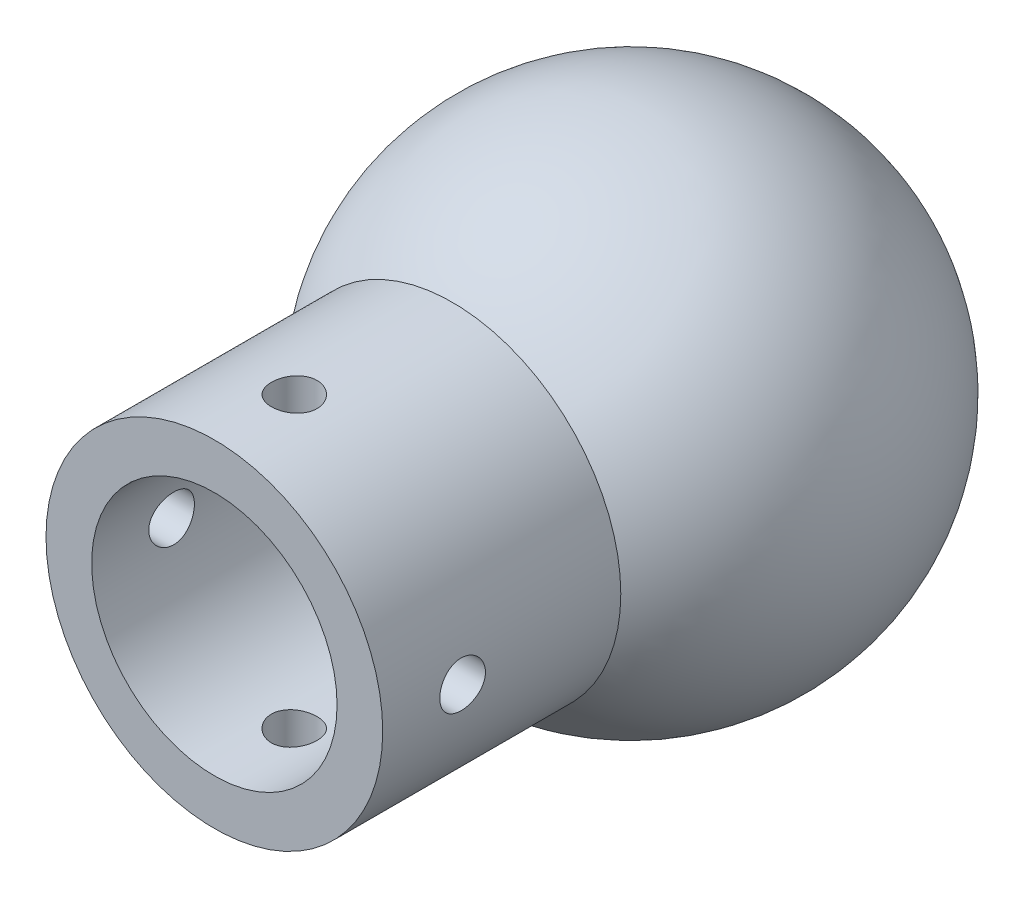
SolidWorks part; units mm, degrees
ref_plane "Front Plane" through (0, 0, 0) normal (0, 0, 1) x (1, 0, 0)
ref_plane "Top Plane" through (0, 0, 0) normal (0, 1, 0) x (1, 0, 0)
ref_plane "Right Plane" through (0, 0, 0) normal (1, 0, 0) x (0, 0, -1)
sketch "Sketch1" plane through (0, 0, 0) normal (0, 0, 1) x (1, 0, 0)
  line L0 (0, 21.5) -> (0, -21.5)
  arc A0 (0, -21.5) -> (0, 21.5) centre (0, 0) ccw
  dimension "D1" = 43
revolve "Revolve1" add sketch "Sketch1" angle 360 about L0
ref_plane "Plane1" through (0, 0, 21.5) normal (0, 0, 1) x (1, 0, 0)
sketch "Sketch2" plane through (0, 0, 21.5) normal (0, 0, 1) x (1, 0, 0)
  circle A0 centre (0, 0) radius 10.75
  dimension "D1" = 21.5
extrude "Cut-Extrude1" cut sketch "Sketch2" against normal blind 15
sketch "Sketch3" plane through (0, 0, 21.5) normal (0, 0, 1) x (1, 0, 0)
  circle A0 centre (0, 0) radius 10.75
  circle A1 centre (0, 0) radius 14.75
  dimension "D1" = 4
extrude "Boss-Extrude1" add sketch "Sketch3" against normal up to surface (2.8805 mm away) up to face at (-10.75, 0, 18.6195)
sketch "Sketch4" plane through (0, 0, 21.5) normal (0, 0, 1) x (1, 0, 0)
  circle A0 centre (0, 0) radius 10.75 construction
  circle A1 centre (0, 0) radius 14.75
  circle A2 centre (0, 0) radius 14.75
  circle A3 centre (0, 0) radius 10.75
  dimension "D1" = 0
extrude "Boss-Extrude2" add sketch "Sketch4" along normal blind 15
sketch "Sketch5" plane through (0, 0, 0) normal (0, 1, 0) x (1, 0, 0)
  line L0 (-14.75, -36.5) -> (14.75, -36.5) construction
  circle A0 centre (0, -29.5) radius 2
  dimension "D1" = 4
  dimension "D2" = 7
extrude "Cut-Extrude2" cut sketch "Sketch5" against normal through all both and the other way through all
sketch "Sketch7" plane through (0, 0, 0) normal (1, 0, 0) x (0, 0, -1)
  line L0 (-36.5, 14.75) -> (-36.5, -14.75) construction
  circle A0 centre (-29.5, 0) radius 2
  dimension "D1" = 4
  dimension "D2" = 7
extrude "Cut-Extrude3" cut sketch "Sketch7" against normal through all both and the other way through all contours A0
